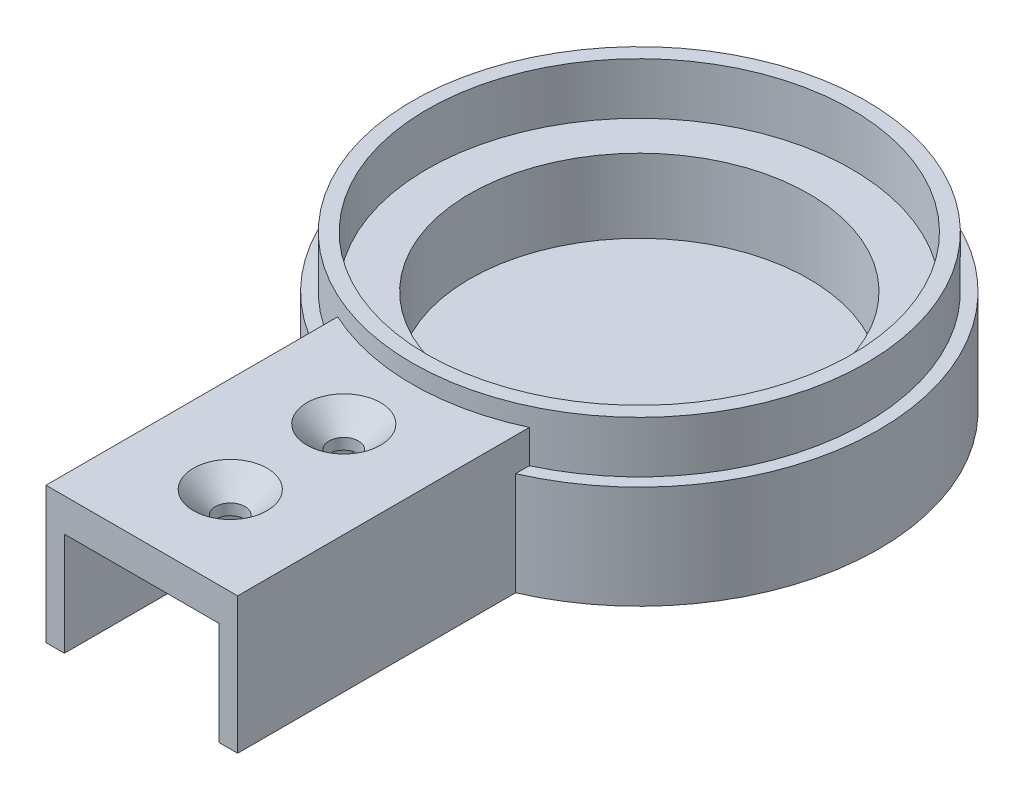
SolidWorks part; units mm, degrees
ref_plane "Plan de face" through (0, 0, 0) normal (0, 0, 1) x (1, 0, 0)
ref_plane "Plan de dessus" through (0, 0, 0) normal (0, 1, 0) x (1, 0, 0)
ref_plane "Plan de droite" through (0, 0, 0) normal (1, 0, 0) x (0, 0, -1)
sketch "Esquisse1" plane through (0, 0, 0) normal (0, 1, 0) x (1, 0, 0)
  circle A0 centre (0, 0) radius 32.5
  dimension "D1" = 65
extrude "Boss.-Extru.1" add sketch "Esquisse1" along normal blind 4
sketch "Esquisse2" plane through (0, 4, 0) normal (0, 1, 0) x (1, 0, 0)
  circle A0 centre (0, 0) radius 23
  circle A1 centre (0, 0) radius 32.5
  circle A2 centre (0, 0) radius 32.5 construction
  dimension "D1" = 46
extrude "Boss.-Extru.2" add sketch "Esquisse2" along normal blind 10
sketch "Esquisse4" plane through (0, 14, 0) normal (0, 1, 0) x (1, 0, 0)
  circle A0 centre (0, 0) radius 28.8
  circle A1 centre (0, 0) radius 30.8
  dimension "D1" = 57.6
  dimension "D2" = 61.6
extrude "Boss.-Extru.4" add sketch "Esquisse4" along normal blind 7
ref_plane "Plan1" through (0, 0, 32.5) normal (0, 0, 1) x (1, 0, 0)
sketch "Esquisse5" plane through (0, 0, 32.5) normal (0, 0, 1) x (1, 0, 0)
  line L1 (13, 18.5) -> (-13, 18.5)
  line L2 (13, 18.5) -> (13, 0)
  line L3 (13, 0) -> (10.5, 0)
  line L4 (-13, 18.5) -> (-13, 0)
  line L5 (0, 18.5) -> (0, 0) construction
  line L6 (-10.5, 0) -> (-13, 0)
  line L8 (-10.5, 0) -> (-10.5, 14)
  line L9 (-10.5, 14) -> (10.5, 14)
  line L10 (10.5, 0) -> (10.5, 14)
  line L11 (0, 14) -> (0, 2.7086) construction
  line L13 (-32.5, 0) -> (32.5, 0) construction
  point P15 (-12.5, 0)
  point P16 (0, 0)
  point P17 (0, 0)
  dimension "D1" = 26
  dimension "D2" = 18.5
  dimension "D3" = 21
  dimension "D4" = 4.5
extrude "Boss.-Extru.5" add sketch "Esquisse5" along normal blind 35 and the other way up to surface other way up to face at (0, 21, 28.8)
sketch "Esquisse6" plane through (0, 18.5, 0) normal (0, 1, 0) x (1, 0, 0)
  line L0 (0, -67.5) -> (0, -32.0251) construction
  line L1 (13, -67.5) -> (-13, -67.5) construction
  line L2 (-10.5, -67.5) -> (10.5, -67.5) construction
  circle A0 centre (0, -55.5) radius 2
  circle A1 centre (0, -40.1) radius 2
  dimension "D1" = 4
  dimension "D2" = 4
  dimension "D3" = 15.4
  dimension "D4" = 12
extrude "Enlèv. mat.-Extru.1" cut sketch "Esquisse6" against normal blind 5
chamfer "Chanfrein1" distance 3 angle 45 2 edges at (-2, 18.5, 40.1) (-2, 18.5, 55.5)
sketch "Esquisse8" plane through (0, 0, 32.5) normal (0, 0, 1) x (1, 0, 0)
  line L0 (-10.5, 0) -> (-10.5, 14) construction
  line L1 (-10.5, 4) -> (-6.5, 4)
  line L2 (-10.5, 4) -> (-10.5, 12)
  line L3 (-10.5, 12) -> (-6.5, 12)
  line L4 (-6.5, 4) -> (-6.5, 12)
  line L6 (-10.5, 0) -> (10.5, 0) construction
  line L7 (10.5, 14) -> (10.5, 0) construction
  line L8 (10.5, 4) -> (6.5, 4)
  line L9 (10.5, 4) -> (10.5, 12)
  line L10 (10.5, 12) -> (6.5, 12)
  line L11 (6.5, 4) -> (6.5, 12)
  line L12 (-10.5, 14) -> (10.5, 14) construction
  dimension "D1" = 4
  dimension "D2" = 4
  dimension "D3" = 4
  dimension "D4" = 2
extrude "Enlèv. mat.-Extru.2" cut sketch "Esquisse8" against normal up to surface (12.0366 mm away)
equation "\"D2@Esquisse4\"=\"D1@Esquisse4\"+4"
equation "\"D4@Esquisse5\"=(\"D1@Esquisse5\"-\"D3@Esquisse5\")/2+2"
equation "\"D2@Esquisse6\"=\"D1@Esquisse6\""
equation "\"D3@Esquisse6\"=18.6-3.2"
equation "\"D2@Esquisse5\"=14+\"D4@Esquisse5\""
equation "\"D3@Esquisse8\"=\"D1@Esquisse8\""
